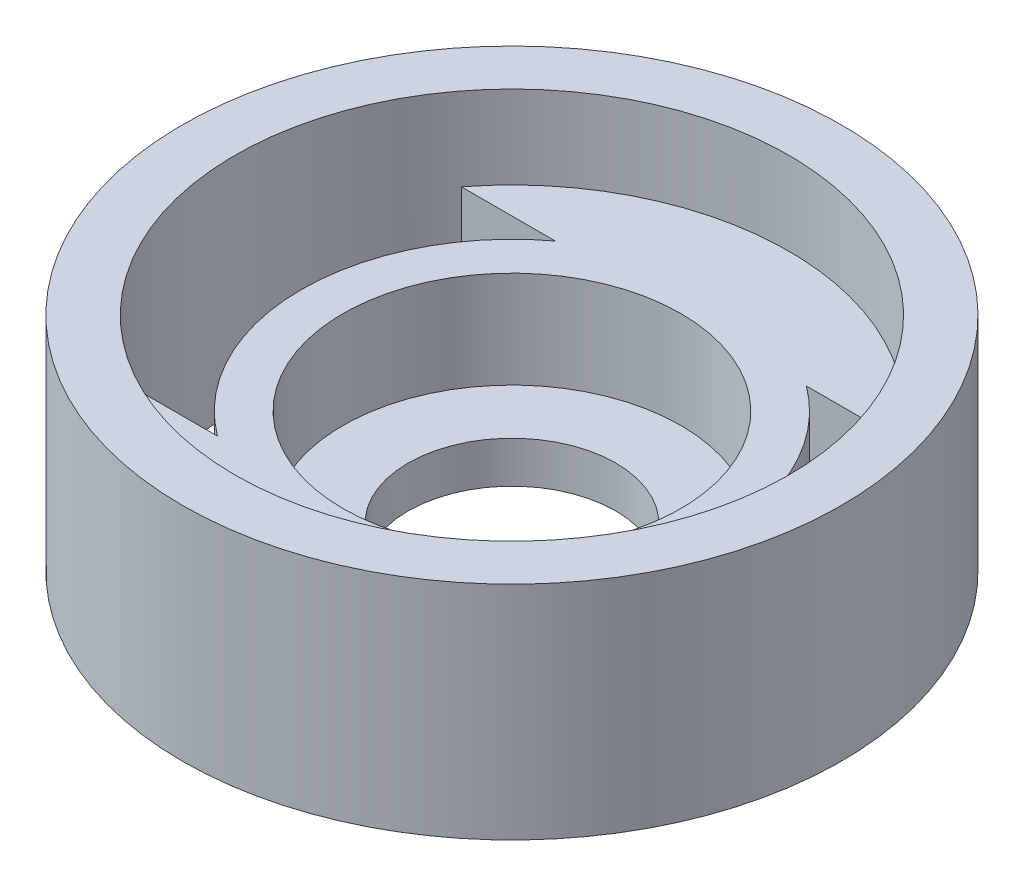
SolidWorks part; units mm, degrees
ref_plane "Front Plane" through (0, 0, 0) normal (0, 0, 1) x (1, 0, 0)
ref_plane "Top Plane" through (0, 0, 0) normal (0, 1, 0) x (1, 0, 0)
ref_plane "Right Plane" through (0, 0, 0) normal (1, 0, 0) x (0, 0, -1)
sketch "Sketch1" plane through (0, 0, 0) normal (0, 1, 0) x (1, 0, 0)
  circle A0 centre (0, 0) radius 23.2
  circle A1 centre (0, 0) radius 12.2
  dimension "D1" = 46.4
  dimension "D2" = 24.4
extrude "Boss-Extrude1" add sketch "Sketch1" along normal blind 10
sketch "Sketch2" plane through (0, 0, 0) normal (0, -1, 0) x (1, 0, 0)
  circle A0 centre (0, 0) radius 12.2 construction
  circle A1 centre (0, 0) radius 12.2
extrude "Boss-Extrude2" add sketch "Sketch2" against normal blind 3
sketch "Sketch3" plane through (0, 3, 0) normal (0, 1, 0) x (1, 0, 0)
  circle A0 centre (0, 0) radius 7.5
  dimension "D1" = 15
extrude "Cut-Extrude1" cut sketch "Sketch3" against normal blind 3
sketch "Sketch4" plane through (0, 10, 0) normal (0, 1, 0) x (1, 0, 0)
  circle A0 centre (0, 0) radius 20
  circle A1 centre (0, 0) radius 23.2 construction
  circle A2 centre (0, 0) radius 23.2
  dimension "D1" = 3.2
extrude "Boss-Extrude3" add sketch "Sketch4" along normal blind 6
sketch "Sketch6" plane through (0, 10, 0) normal (0, 1, 0) x (1, 0, 0)
  line L0 (0, 12.2) -> (15.848, 12.2)
  line L1 (15.848, 12.2) -> (-15.848, 12.2)
  line L2 (15.848, -12.2) -> (-15.848, -12.2)
  circle A0 centre (0, 0) radius 12.2 construction
  circle A1 centre (0, 0) radius 20
  circle A2 centre (0, 0) radius 20
  circle A3 centre (0, 0) radius 12.2
  circle A4 centre (0, 0) radius 15.2
  dimension "D1" = 0
  dimension "D2" = 3
extrude "Cut-Extrude3" cut sketch "Sketch6" against normal blind 59 contours A4 L1 L2 | A4 L2 L1
sketch "Sketch8" plane through (0, 16, 0) normal (0, 1, 0) x (1, 0, 0)
  circle A0 centre (0, 0) radius 23.2 construction
  circle A1 centre (0, 0) radius 23.2
  circle A2 centre (0, 0) radius 23.8
  dimension "D1" = 0.6
extrude "Boss-Extrude4" add sketch "Sketch8" against normal up to surface (16 mm away) up to face at (15.0286, 0, 0)
